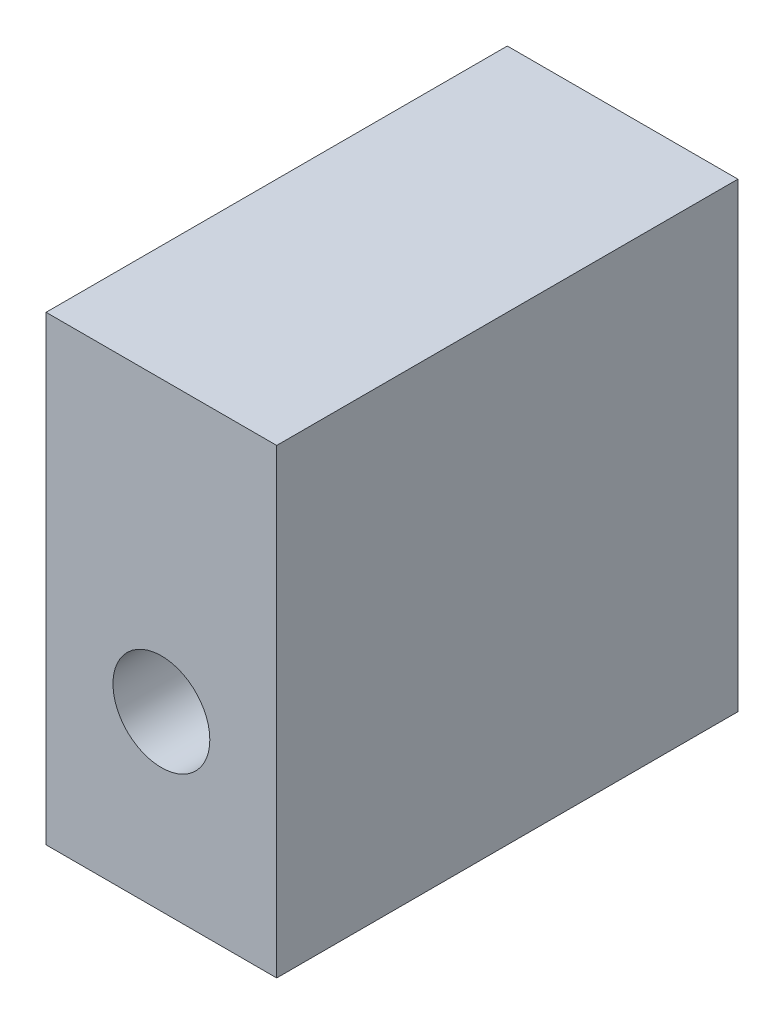
SolidWorks part; units mm, degrees
ref_plane "Front Plane" through (0, 0, 0) normal (0, 0, 1) x (1, 0, 0)
ref_plane "Top Plane" through (0, 0, 0) normal (0, 1, 0) x (1, 0, 0)
ref_plane "Right Plane" through (0, 0, 0) normal (1, 0, 0) x (0, 0, -1)
sketch "Sketch1" plane through (0, 0, 0) normal (0, 1, 0) x (1, 0, 0)
  line L1 (-25.4, -50.8) -> (25.4, -50.8)
  line L2 (-25.4, -50.8) -> (-25.4, 50.8)
  line L3 (-25.4, 50.8) -> (25.4, 50.8)
  line L4 (25.4, -50.8) -> (25.4, 50.8)
  line L5 (-25.4, -50.8) -> (25.4, 50.8) construction
  line L6 (-25.4, 50.8) -> (25.4, -50.8) construction
  point P0 (0, 0)
  dimension "D1" = 101.6
  dimension "D2" = 50.8
extrude "Boss-Extrude2" add sketch "Sketch1" along normal blind 101.6
sketch "Sketch4" plane through (0, 0, 0) normal (0, 0, 1) x (1, 0, 0)
  circle A0 centre (0, 38.1) radius 10.668
  dimension "D1" = 21.336
  dimension "D2" = 38.1
extrude "Cut-Extrude2" cut sketch "Sketch4" against normal through all both and the other way through all
